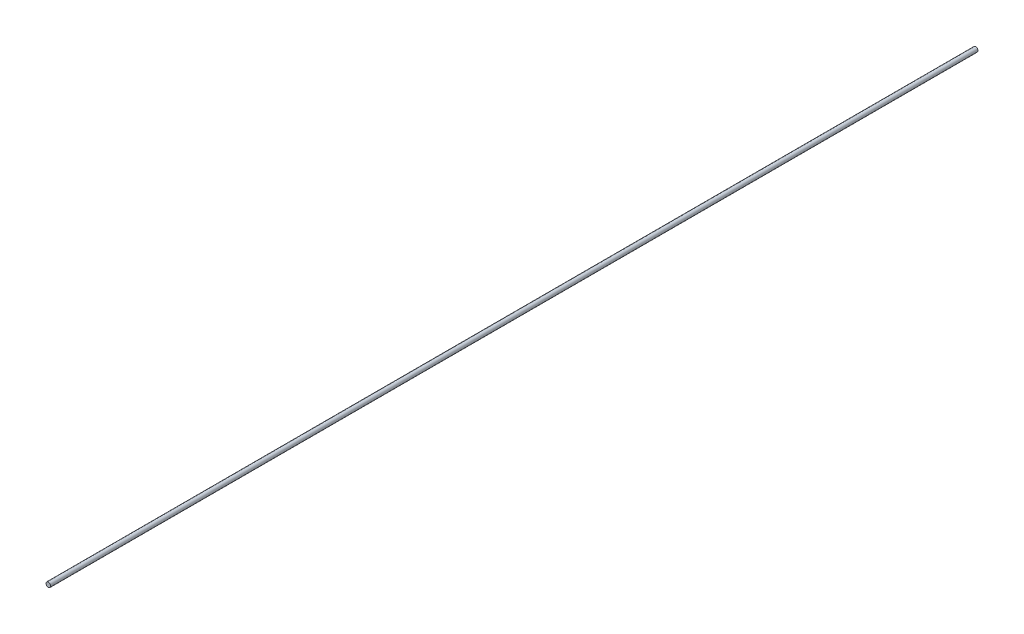
SolidWorks part; units mm, degrees
material "Hexcel AS4C (3000 Filaments)"
ref_plane "Front Plane" through (0, 0, 0) normal (0, 0, 1) x (1, 0, 0)
ref_plane "Top Plane" through (0, 0, 0) normal (0, 1, 0) x (1, 0, 0)
ref_plane "Right Plane" through (0, 0, 0) normal (1, 0, 0) x (0, 0, -1)
sketch "Sketch1" plane through (0, 0, 0) normal (0, 0, 1) x (1, 0, 0)
  circle A0 centre (0, 0) radius 2.54 construction
  circle A1 centre (0, 0) radius 2.54
extrude "Boss-Extrude1" add sketch "Sketch1" along normal blind 1016
